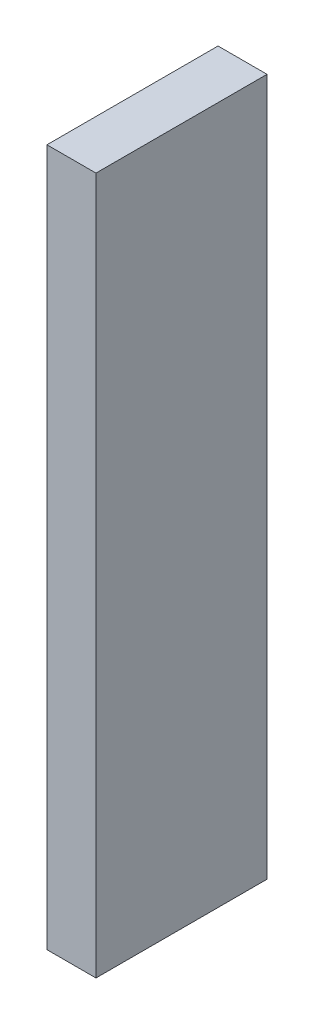
SolidWorks part; units mm, degrees
material "1023 al carbonio, lamiera (SS)"
ref_plane "Piano frontale" through (0, 0, 0) normal (0, 0, 1) x (1, 0, 0)
ref_plane "Piano superiore" through (0, 0, 0) normal (0, 1, 0) x (1, 0, 0)
ref_plane "Piano destro" through (0, 0, 0) normal (1, 0, 0) x (0, 0, -1)
sketch "Schizzo1" plane through (0, 0, 0) normal (0, 0, 1) x (1, 0, 0)
  line L0 (2.25, 64) -> (2.25, 0) construction
  line L1 (0, 0) -> (4.5, 0)
  line L2 (0, 0) -> (0, 64)
  line L3 (0, 64) -> (4.5, 64)
  line L4 (4.5, 0) -> (4.5, 64)
  dimension "D1" = 64
  dimension "D2" = 4.5
extrude "Estrusione-Estrusione1" add sketch "Schizzo1" along normal blind 15.707
